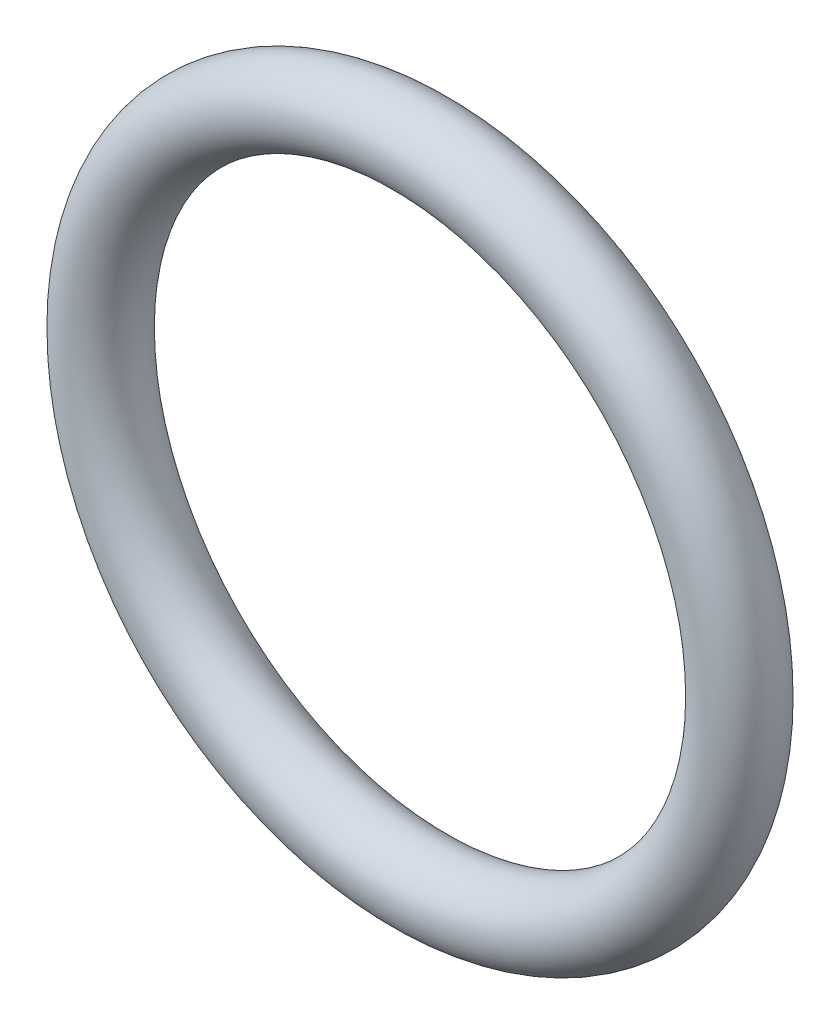
SolidWorks part; units mm, degrees
ref_plane "Front" through (0, 0, 0) normal (0, 0, 1) x (1, 0, 0)
ref_plane "Top" through (0, 0, 0) normal (0, 1, 0) x (1, 0, 0)
ref_plane "Right" through (0, 0, 0) normal (1, 0, 0) x (0, 0, -1)
sketch "Sketch1" plane through (0, 0, 0) normal (1, 0, 0) x (0, -1, 0)
  line L0 (0, -1.1049) -> (0, 1.1049) construction
  line L2 (-11.4275, 0) -> (11.4275, 0) construction
  line L3 (-8.1788, 0) -> (8.1788, 0) construction
  circle A0 centre (9.2837, 0) radius 1.1049
  point P9 (8.1788, 0)
  point P10 (10.3886, 0)
  point P13 (9.2837, 1.1049)
  point P14 (9.2837, -1.1049)
  dimension "Width" = 2.2098
  dimension "ID" = 16.3576
revolve "Revolve1" add sketch "Sketch1" angle 360 about L0
